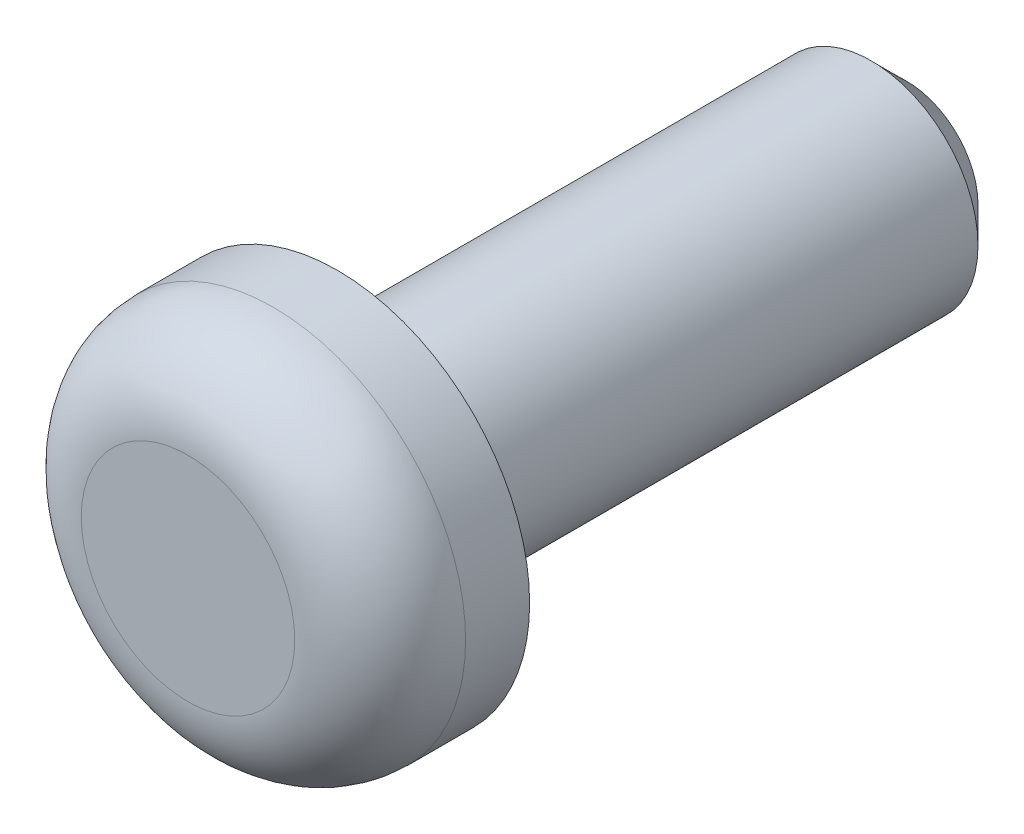
SolidWorks part; units mm, degrees
ref_plane "Vorne" through (0, 0, 0) normal (0, 0, 1) x (1, 0, 0)
ref_plane "Oben" through (0, 0, 0) normal (0, 1, 0) x (1, 0, 0)
ref_plane "Rechts" through (0, 0, 0) normal (1, 0, 0) x (0, 0, -1)
sketch "Skizze1" plane through (0, 0, 0) normal (1, 0, 0) x (0, 0, -1)
  line L0 (0, 2.7) -> (0, 1.5)
  line L1 (0, 1.5) -> (8, 1.5)
  line L2 (8, 1.5) -> (8, 0)
  line L3 (8, 0) -> (-2.1, 0)
  line L4 (-2.1, 0) -> (-2.1, 2.7)
  line L5 (0, 2.7) -> (-2.1, 2.7)
  line L6 (0, 0) -> (16.053, 0) construction
  dimension "D1" = 3
  dimension "D2" = 8
  dimension "D3" = 2.1
  dimension "D4" = 5.4
revolve "Rotation1" add sketch "Skizze1" angle 360 about L6
fillet "Verrundung1" radius 1.2 1 edges at (2.7, 0, 2.1)
chamfer "Fase1" distance 0.5 angle 45 1 edges at (1.5, 0, -8)
